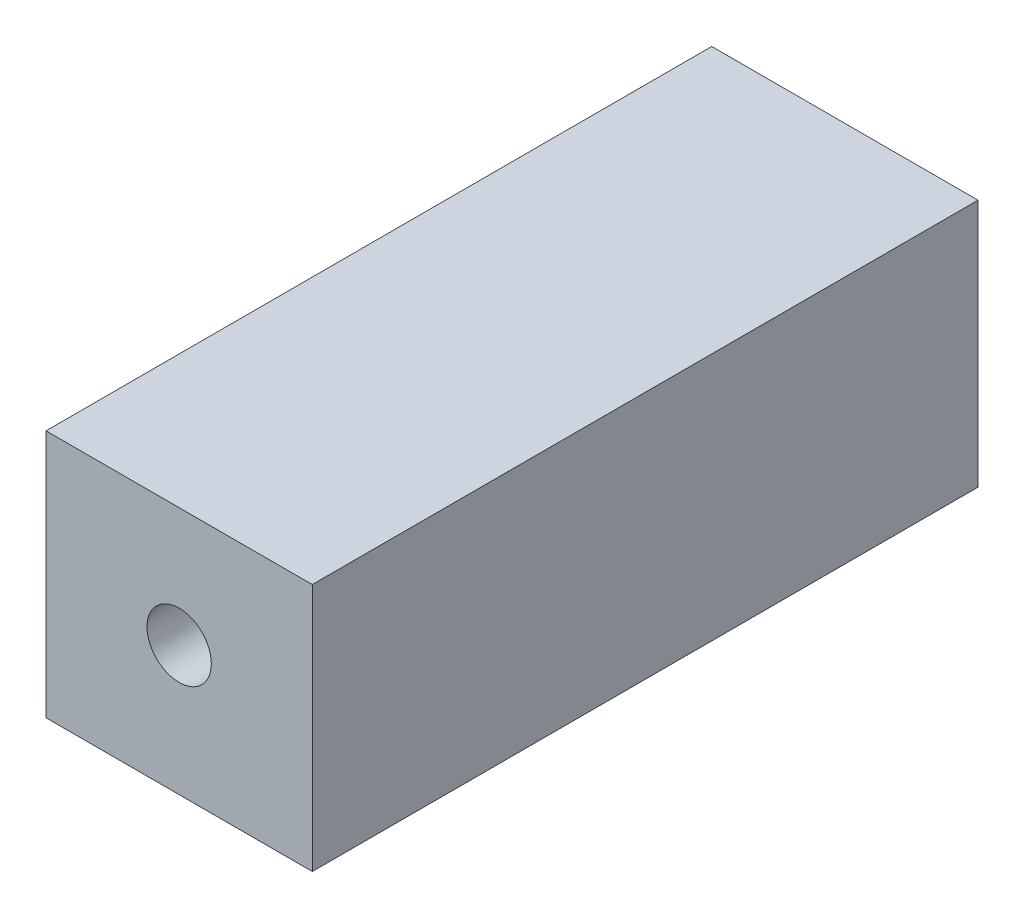
SolidWorks part; units mm, degrees
ref_plane "Front Plane" through (0, 0, 0) normal (0, 0, 1) x (1, 0, 0)
ref_plane "Top Plane" through (0, 0, 0) normal (0, 1, 0) x (1, 0, 0)
ref_plane "Right Plane" through (0, 0, 0) normal (1, 0, 0) x (0, 0, -1)
sketch "Sketch1" plane through (0, 0, 0) normal (0, 0, 1) x (1, 0, 0)
  line L0 (0, 0) -> (6, 0) construction
  line L1 (0, 0) -> (0, 5.37) construction
  line L2 (0, 0) -> (0, -5.83) construction
  line L3 (0, 0) -> (-6, 0) construction
  line L5 (6, -5.83) -> (-6, -5.83)
  line L6 (6, -5.83) -> (6, 5.37)
  line L7 (6, 5.37) -> (-6, 5.37)
  line L8 (-6, -5.83) -> (-6, 5.37)
  circle A0 centre (0, 0) radius 1.45
  dimension "D1" = 2.9
  dimension "D2" = 6
  dimension "D3" = 5.37
  dimension "D4" = 5.83
  dimension "D5" = 6
extrude "Boss-Extrude1" add sketch "Sketch1" along normal blind 30
